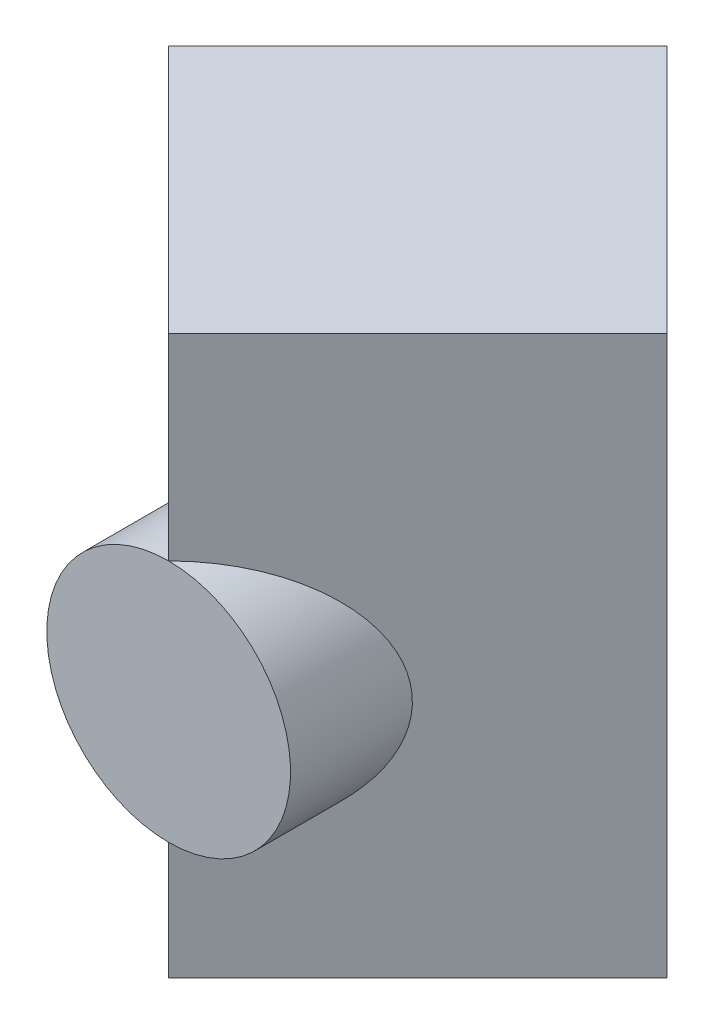
SolidWorks part; units mm, degrees
ref_plane "Front Plane" through (0, 0, 0) normal (0, 0, 1) x (1, 0, 0)
ref_plane "Top Plane" through (0, 0, 0) normal (0, 1, 0) x (1, 0, 0)
ref_plane "Right Plane" through (0, 0, 0) normal (1, 0, 0) x (0, 0, -1)
sketch "Sketch2" plane through (0, 0, 0) normal (0, 1, 0) x (1, 0, 0)
  line L0 (-84.8528, 0) -> (0, -84.8528)
  line L1 (0, -84.8528) -> (84.8528, 0)
  line L2 (84.8528, 0) -> (0, 84.8528)
  line L3 (0, 84.8528) -> (-84.8528, 0)
  line L4 (-84.8528, 0) -> (84.8528, 0) construction
  line L5 (0, 84.8528) -> (0, -84.8528) construction
  point P0 (0, 0)
  point P5 (0, 0)
  point P7 (0, 0)
  dimension "D1" = 120
extrude "Boss-Extrude1" add sketch "Sketch2" along normal mid plane 190
ref_plane "Plane1" through (0, 0, 84.8528) normal (0, 0, 1) x (1, 0, 0)
sketch "Sketch3" plane through (0, 0, 84.8528) normal (0, 0, 1) x (1, 0, 0)
  line L0 (0, 95) -> (0, -95) construction
  line L1 (-1000, -55) -> (49000, -55) construction
  circle A0 centre (0, -13.5) radius 41.5
  dimension "D1" = 83
  dimension "D2" = 40
extrude "Boss-Extrude3" add sketch "Sketch3" against normal blind 45
